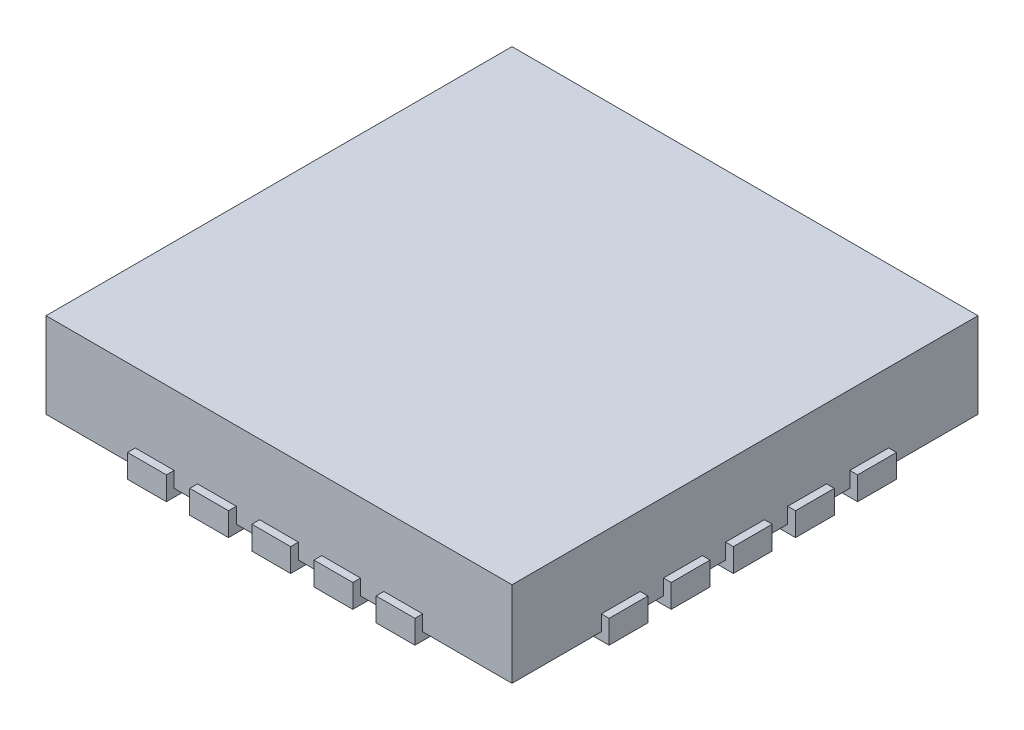
SolidWorks part; units mm, degrees
ref_plane "Front Plane" through (0, 0, 0) normal (0, 0, 1) x (1, 0, 0)
ref_plane "Top Plane" through (0, 0, 0) normal (0, 1, 0) x (1, 0, 0)
ref_plane "Right Plane" through (0, 0, 0) normal (1, 0, 0) x (0, 0, -1)
sketch "Sketch1" plane through (0, 0, 0) normal (0, 1, 0) x (1, 0, 0)
  line L1 (-1.5, 1.5) -> (1.5, 1.5)
  line L2 (-1.5, 1.5) -> (-1.5, -1.5)
  line L3 (-1.5, -1.5) -> (1.5, -1.5)
  line L4 (1.5, 1.5) -> (1.5, -1.5)
  line L5 (-1.5, 1.5) -> (1.5, -1.5) construction
  line L6 (-1.5, -1.5) -> (1.5, 1.5) construction
  point P0 (0, 0)
  dimension "D1" = 3
  dimension "D2" = 3
extrude "Boss-Extrude1" add sketch "Sketch1" along normal blind 0.55 contours L2 L3 L4 L1
sketch "Sketch2" plane through (0, 0, 0) normal (0, -1, 0) x (1, 0, 0)
  line L0 (0, 1.5) -> (0, -1.5) construction
  line L1 (-1.5, 1.5) -> (1.5, 1.5) construction
  line L2 (-1.5, -1.5) -> (1.5, -1.5) construction
  line L3 (-0.125, 1.5) -> (-0.125, 1.1155)
  line L4 (-0.525, 1.5) -> (-0.525, 1.1155)
  line L5 (-0.4, 1.5) -> (-0.4, 0.9905) construction
  line L6 (-0.275, 1.5) -> (-0.275, 1.1155)
  line L7 (-0.675, 1.5) -> (-0.675, 1.1155)
  line L8 (-0.925, 1.5) -> (-0.925, 1.1155)
  line L9 (-1.5, 1.5) -> (0, 0) construction
  line L10 (0.125, 1.5) -> (0.125, 1.1155)
  line L11 (0.275, 1.5) -> (0.275, 1.1155)
  line L12 (0.525, 1.5) -> (0.525, 1.1155)
  line L13 (0.675, 1.5) -> (0.675, 1.1155)
  line L14 (0.925, 1.5) -> (0.925, 1.1155)
  line L15 (-0.925, 1.5) -> (-0.675, 1.5)
  line L16 (-0.525, 1.5) -> (-0.275, 1.5)
  line L17 (-0.125, 1.5) -> (0.125, 1.5)
  line L18 (0.275, 1.5) -> (0.525, 1.5)
  line L19 (0.675, 1.5) -> (0.925, 1.5)
  line L20 (-1.5, 0) -> (1.5, 0) construction
  line L21 (-1.5, -1.5) -> (-1.5, 1.5) construction
  line L22 (1.5, -1.5) -> (1.5, 1.5) construction
  line L23 (0.125, 1.5) -> (-0.125, 1.5)
  line L24 (0.125, 1.5) -> (0.125, 1.1155)
  line L25 (-0.125, 1.5) -> (-0.125, 1.1155)
  line L26 (-0.525, 1.5) -> (-0.525, 1.1155)
  line L27 (-0.275, 1.5) -> (-0.275, 1.1155)
  line L28 (-0.675, 1.5) -> (-0.675, 1.1155)
  line L29 (-0.125, 1.5) -> (-0.125, 1.1155)
  line L30 (-0.525, 1.5) -> (-0.525, 1.1155)
  line L31 (-0.275, 1.5) -> (-0.275, 1.1155)
  line L32 (-0.675, 1.5) -> (-0.675, 1.1155)
  line L33 (0.125, 1.5) -> (-0.125, 1.5)
  line L34 (0.125, 1.5) -> (0.125, 1.1155)
  line L35 (-0.125, 1.5) -> (-0.125, 1.1155)
  line L36 (-0.525, 1.5) -> (-0.525, 1.1155)
  line L37 (-0.275, 1.5) -> (-0.275, 1.1155)
  line L38 (-0.675, 1.5) -> (-0.675, 1.1155)
  line L39 (-0.125, 1.5) -> (-0.125, 1.1155)
  line L40 (-0.525, 1.5) -> (-0.525, 1.1155)
  line L41 (-0.275, 1.5) -> (-0.275, 1.1155)
  line L42 (-0.675, 1.5) -> (-0.675, 1.1155)
  line L43 (-0.125, 1.5) -> (-0.125, 1.1155)
  line L44 (-0.525, 1.5) -> (-0.525, 1.1155)
  line L45 (-0.275, 1.5) -> (-0.275, 1.1155)
  line L46 (-0.675, 1.5) -> (-0.675, 1.1155)
  line L47 (-0.125, 1.5) -> (-0.125, 1.1155)
  line L48 (-0.525, 1.5) -> (-0.525, 1.1155)
  line L49 (-0.275, 1.5) -> (-0.275, 1.1155)
  line L50 (-0.675, 1.5) -> (-0.675, 1.1155)
  line L51 (0.125, 1.5) -> (-0.125, 1.5)
  line L52 (0.125, 1.5) -> (0.125, 1.1155)
  line L53 (-0.125, 1.5) -> (-0.125, 1.1155)
  line L54 (-0.525, 1.5) -> (-0.525, 1.1155)
  line L55 (-0.275, 1.5) -> (-0.275, 1.1155)
  line L56 (-0.675, 1.5) -> (-0.675, 1.1155)
  line L57 (-1.5, 0.125) -> (-1.5, -0.125)
  line L58 (-1.5, 0.675) -> (-1.1155, 0.675)
  line L59 (-1.5, 0.525) -> (-1.1155, 0.525)
  line L60 (-1.5, 0.125) -> (-1.1155, 0.125)
  line L61 (-1.5, 0.275) -> (-1.1155, 0.275)
  line L62 (-1.5, 0.525) -> (-1.5, 0.275)
  line L63 (-1.5, 0.925) -> (-1.5, 0.675)
  line L64 (-1.5, 0.925) -> (-1.1155, 0.925)
  line L65 (0.925, -1.5) -> (0.925, -1.1155)
  line L66 (0.675, -1.5) -> (0.925, -1.5)
  line L67 (0.675, -1.5) -> (0.675, -1.1155)
  line L68 (0.525, -1.5) -> (0.525, -1.1155)
  line L69 (0.275, -1.5) -> (0.525, -1.5)
  line L70 (0.275, -1.5) -> (0.275, -1.1155)
  line L71 (-0.125, -1.5) -> (-0.125, -1.1155)
  line L72 (-0.125, -1.5) -> (0.125, -1.5)
  line L73 (0.125, -1.5) -> (0.125, -1.1155)
  line L74 (-0.525, -1.5) -> (-0.525, -1.1155)
  line L75 (-0.275, -1.5) -> (-0.275, -1.1155)
  line L76 (-0.525, -1.5) -> (-0.275, -1.5)
  line L77 (-0.925, -1.5) -> (-0.675, -1.5)
  line L78 (-0.675, -1.5) -> (-0.675, -1.1155)
  line L79 (-0.925, -1.5) -> (-0.925, -1.1155)
  line L80 (-1.5, -0.925) -> (-1.5, -0.675)
  line L81 (-1.5, -0.925) -> (-1.1155, -0.925)
  line L82 (-1.5, -0.675) -> (-1.1155, -0.675)
  line L83 (-1.5, -0.525) -> (-1.1155, -0.525)
  line L84 (-1.5, -0.525) -> (-1.5, -0.275)
  line L85 (-1.5, -0.275) -> (-1.1155, -0.275)
  line L86 (-1.5, -0.125) -> (-1.1155, -0.125)
  line L87 (1.5, -0.125) -> (1.1155, -0.125)
  line L88 (1.5, -0.275) -> (1.1155, -0.275)
  line L89 (1.5, -0.525) -> (1.5, -0.275)
  line L90 (1.5, -0.525) -> (1.1155, -0.525)
  line L91 (1.5, -0.675) -> (1.1155, -0.675)
  line L92 (1.5, -0.925) -> (1.1155, -0.925)
  line L93 (1.5, -0.925) -> (1.5, -0.675)
  line L94 (1.5, 0.925) -> (1.1155, 0.925)
  line L95 (1.5, 0.925) -> (1.5, 0.675)
  line L96 (1.5, 0.525) -> (1.5, 0.275)
  line L97 (1.5, 0.275) -> (1.1155, 0.275)
  line L98 (1.5, 0.125) -> (1.1155, 0.125)
  line L99 (1.5, 0.525) -> (1.1155, 0.525)
  line L100 (1.5, 0.675) -> (1.1155, 0.675)
  line L101 (1.5, 0.125) -> (1.5, -0.125)
  arc A0 (-0.125, 1.1155) -> (0.125, 1.1155) centre (0, 1.1155) ccw
  arc A1 (-0.525, 1.1155) -> (-0.275, 1.1155) centre (-0.4, 1.1155) ccw
  arc A2 (-0.925, 1.1155) -> (-0.675, 1.1155) centre (-0.8, 1.1155) ccw
  arc A3 (0.525, 1.1155) -> (0.275, 1.1155) centre (0.4, 1.1155) cw
  arc A4 (0.925, 1.1155) -> (0.675, 1.1155) centre (0.8, 1.1155) cw
  arc A5 (-0.675, 1.1155) -> (-0.925, 1.1155) centre (-0.8, 1.1155) cw
  arc A6 (0.125, 1.1155) -> (-0.125, 1.1155) centre (0, 1.1155) cw
  arc A7 (-0.675, 1.1155) -> (-0.925, 1.1155) centre (-0.8, 1.1155) cw
  arc A8 (-0.125, 1.1155) -> (0.125, 1.1155) centre (0, 1.1155) ccw
  arc A9 (0.125, 1.1155) -> (-0.125, 1.1155) centre (0, 1.1155) cw
  arc A10 (-0.675, 1.1155) -> (-0.925, 1.1155) centre (-0.8, 1.1155) cw
  arc A11 (-0.125, 1.1155) -> (0.125, 1.1155) centre (0, 1.1155) ccw
  arc A12 (-0.125, 1.1155) -> (0.125, 1.1155) centre (0, 1.1155) ccw
  arc A13 (0.125, 1.1155) -> (-0.125, 1.1155) centre (0, 1.1155) cw
  arc A14 (-1.1155, 0.925) -> (-1.1155, 0.675) centre (-1.1155, 0.8) cw
  arc A15 (-1.1155, 0.525) -> (-1.1155, 0.275) centre (-1.1155, 0.4) cw
  arc A16 (-1.1155, 0.125) -> (-1.1155, -0.125) centre (-1.1155, 0) cw
  arc A17 (0.925, -1.1155) -> (0.675, -1.1155) centre (0.8, -1.1155) ccw
  arc A18 (0.525, -1.1155) -> (0.275, -1.1155) centre (0.4, -1.1155) ccw
  arc A19 (-0.125, -1.1155) -> (0.125, -1.1155) centre (0, -1.1155) cw
  arc A20 (-0.525, -1.1155) -> (-0.275, -1.1155) centre (-0.4, -1.1155) cw
  arc A21 (-0.925, -1.1155) -> (-0.675, -1.1155) centre (-0.8, -1.1155) cw
  arc A22 (-1.1155, -0.925) -> (-1.1155, -0.675) centre (-1.1155, -0.8) ccw
  arc A23 (-1.1155, -0.525) -> (-1.1155, -0.275) centre (-1.1155, -0.4) ccw
  arc A24 (1.1155, -0.525) -> (1.1155, -0.275) centre (1.1155, -0.4) cw
  arc A25 (1.1155, -0.925) -> (1.1155, -0.675) centre (1.1155, -0.8) cw
  arc A26 (1.1155, 0.125) -> (1.1155, -0.125) centre (1.1155, 0) ccw
  arc A27 (1.1155, 0.525) -> (1.1155, 0.275) centre (1.1155, 0.4) ccw
  arc A28 (1.1155, 0.925) -> (1.1155, 0.675) centre (1.1155, 0.8) ccw
  line M5 (-1.5, -1.5) -> (1.5, -1.5)
  line M6 (1.5, -1.5) -> (1.5, 1.5)
  line M7 (1.5, 1.5) -> (-1.5, 1.5)
  line M8 (-1.5, 1.5) -> (-1.5, -1.5)
  dimension "D1" = 0.125
  dimension "D3" = 0.4
  dimension "D2" = 2
extrude "Boss-Extrude2" add sketch "Sketch2" along normal blind 0.05 contours L81 A22 L82 M8 | L83 A23 L85 M8 | A15 L59 L61 M8 | A14 L64 L58 M8 | L8 A2 L7 M7 | L4 A1 L6 M7 | L3 A0 L10 M7 | A3 L12 L11 M7 | A4 L14 L13 M7 | L94 A28 L100 M6 | L99 A27 L97 M6 | L98 A26 L87 M6 | A24 L90 L88 M6 | A25 L92 L91 M6 | L65 A17 L67 M5 | L68 A18 L70 M5 | A19 L71 L73 M5 | A20 L74 L75 M5 | A21 L79 L78 M5 | L86 A16 L60 L57
sketch "Sketch3" plane through (-1.5, 0, 0) normal (-1, 0, 0) x (0, 0, 1)
  line L0 (-0.925, 0.1) -> (-0.925, -0.05)
  line L1 (-0.675, -0.05) -> (-0.925, -0.05) construction
  line L2 (-0.925, -0.05) -> (-0.675, -0.05)
  line L3 (-0.675, 0.1) -> (-0.925, 0.1)
  line L5 (-0.675, -0.05) -> (-0.675, 0.1)
  line L6 (-0.525, 0.1) -> (-0.525, -0.05)
  line L7 (-0.275, 0.1) -> (-0.525, 0.1)
  line L8 (-0.275, -0.05) -> (-0.275, 0.1)
  line L9 (-0.525, -0.05) -> (-0.275, -0.05)
  line L10 (-0.125, 0.1) -> (-0.125, -0.05)
  line L11 (0.125, 0.1) -> (-0.125, 0.1)
  line L12 (0.125, -0.05) -> (0.125, 0.1)
  line L13 (-0.125, -0.05) -> (0.125, -0.05)
  line L14 (0.275, 0.1) -> (0.275, -0.05)
  line L15 (0.525, 0.1) -> (0.275, 0.1)
  line L16 (0.525, -0.05) -> (0.525, 0.1)
  line L17 (0.275, -0.05) -> (0.525, -0.05)
  line L18 (0.675, 0.1) -> (0.675, -0.05)
  line L19 (0.925, 0.1) -> (0.675, 0.1)
  line L20 (0.925, -0.05) -> (0.925, 0.1)
  line L21 (0.675, -0.05) -> (0.925, -0.05)
  dimension "D1" = 0.15
  dimension "D2" = 5
extrude "Boss-Extrude3" add sketch "Sketch3" along normal blind 0.05
ref_plane "Plane1" through (0, 0, 0) normal (-1, 0, 0) x (0, 0, 1)
ref_plane "Plane2" through (0, 0, 0) normal (0, 0, 1) x (1, 0, 0)
ref_plane "Plane3" through (0, 0, 0) normal (0.7071, 0, 0.7071) x (0.7071, 0, -0.7071)
mirror "Mirror1" about plane through (0, 0, 0) normal (-1, 0, 0) of "Boss-Extrude3"
mirror "Mirror2" about plane through (0, 0, 0) normal (0.7071, 0, 0.7071) of "Boss-Extrude3"
mirror "Mirror3" about plane through (0, 0, 0) normal (0, 0, 1) of "Mirror2"
